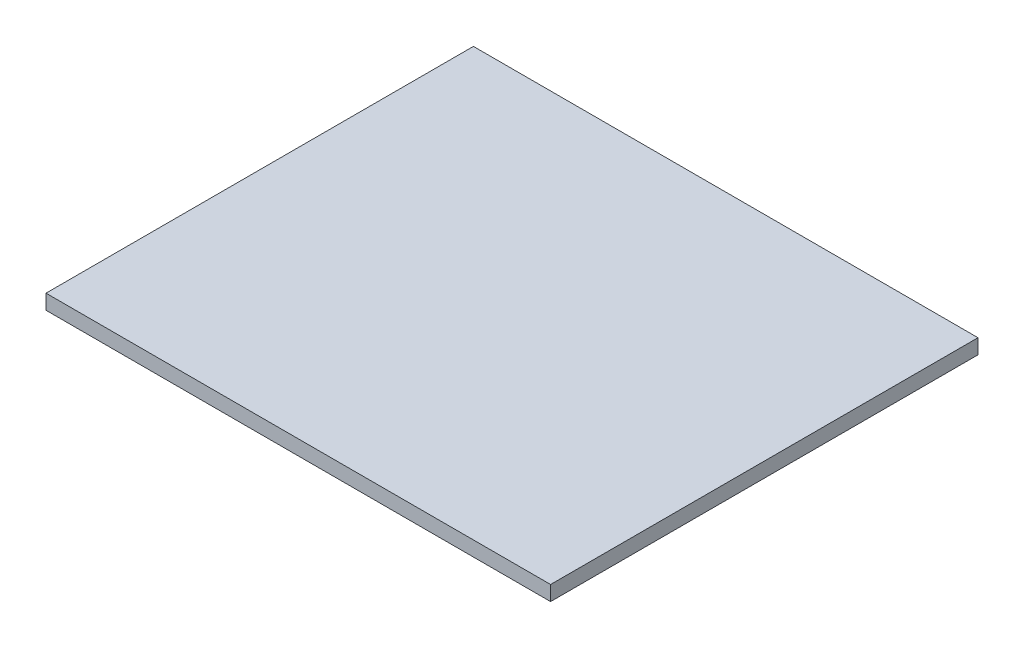
SolidWorks part; units mm, degrees
ref_plane "Front Plane" through (0, 0, 0) normal (0, 0, 1) x (1, 0, 0)
ref_plane "Top Plane" through (0, 0, 0) normal (0, 1, 0) x (1, 0, 0)
ref_plane "Right Plane" through (0, 0, 0) normal (1, 0, 0) x (0, 0, -1)
sketch "Sketch1" plane through (0, 0, 0) normal (0, 1, 0) x (1, 0, 0)
  line L1 (-107.95, 91.44) -> (107.95, 91.44)
  line L2 (-107.95, 91.44) -> (-107.95, -91.44)
  line L3 (-107.95, -91.44) -> (107.95, -91.44)
  line L4 (107.95, 91.44) -> (107.95, -91.44)
  line L5 (-107.95, 91.44) -> (107.95, -91.44) construction
  line L6 (-107.95, -91.44) -> (107.95, 91.44) construction
  point P0 (0, 0)
  dimension "D1" = 215.9
  dimension "D2" = 182.88
extrude "Boss-Extrude1" add sketch "Sketch1" along normal blind 6.35
